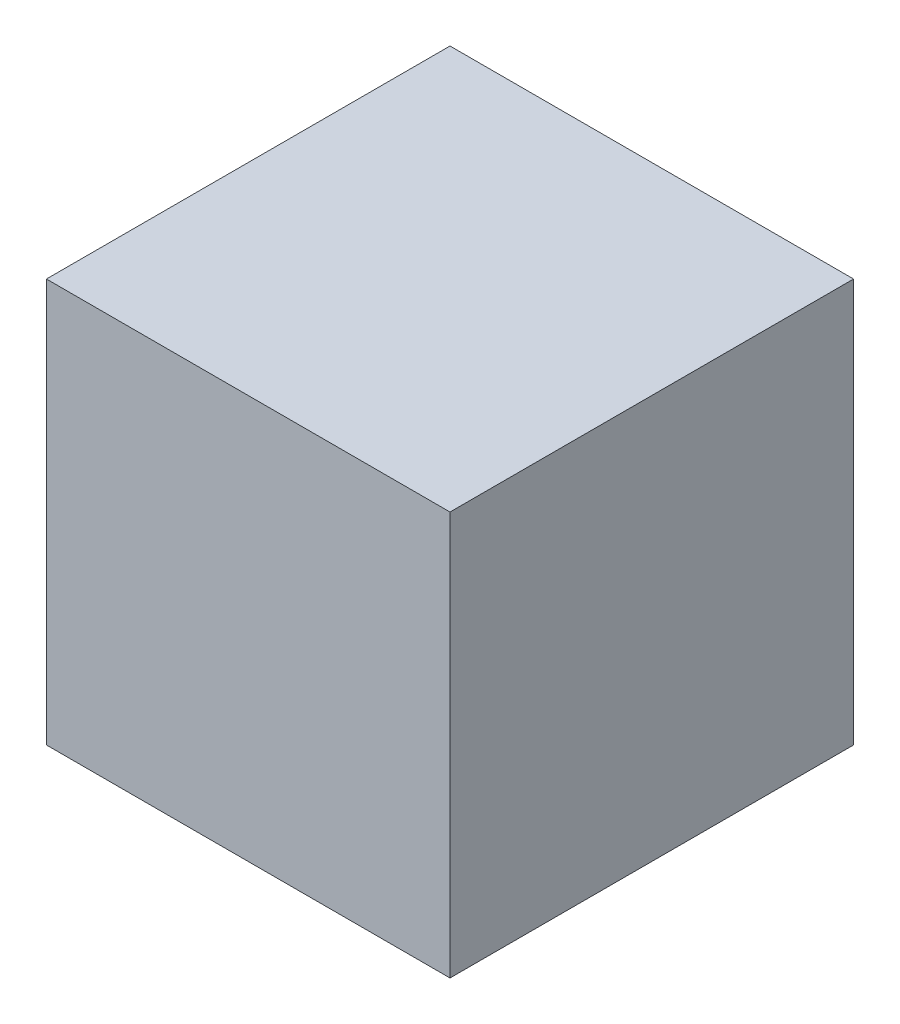
SolidWorks part; units mm, degrees
ref_plane "Front" through (0, 0, 0) normal (0, 0, 1) x (1, 0, 0)
ref_plane "Top" through (0, 0, 0) normal (0, 1, 0) x (1, 0, 0)
ref_plane "Right" through (0, 0, 0) normal (1, 0, 0) x (0, 0, -1)
sketch "Sketch1" plane through (0, 0, 0) normal (0, 1, 0) x (1, 0, 0)
  line L1 (-12.5, -12.5) -> (12.5, -12.5)
  line L2 (-12.5, -12.5) -> (-12.5, 12.5)
  line L3 (-12.5, 12.5) -> (12.5, 12.5)
  line L4 (12.5, -12.5) -> (12.5, 12.5)
  line L5 (-12.5, -12.5) -> (12.5, 12.5) construction
  line L6 (-12.5, 12.5) -> (12.5, -12.5) construction
  point P0 (0, 0)
  dimension "D1" = 25
  dimension "D2" = 25
extrude "Boss-Extrude1" add sketch "Sketch1" along normal blind 25 contours L3 L4 L1 L2
